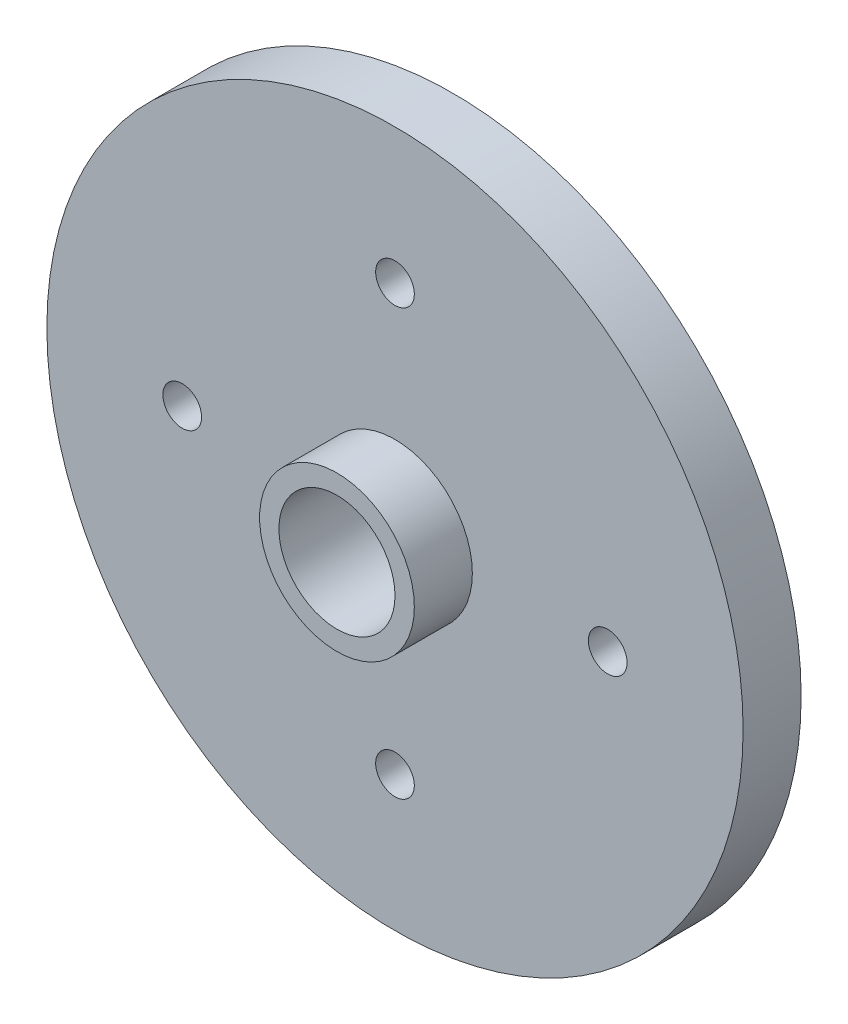
SolidWorks part; units mm, degrees
ref_plane "Front Plane" through (0, 0, 0) normal (0, 0, 1) x (1, 0, 0)
ref_plane "Top Plane" through (0, 0, 0) normal (0, 1, 0) x (1, 0, 0)
ref_plane "Right Plane" through (0, 0, 0) normal (1, 0, 0) x (0, 0, -1)
sketch "Sketch1" plane through (0, 0, 0) normal (0, 0, 1) x (1, 0, 0)
  circle A0 centre (0, 0) radius 18
  circle A1 centre (0, 11) radius 1
  circle A2 centre (11, 0) radius 1
  circle A3 centre (0, -11) radius 1
  circle A4 centre (-11, 0) radius 1
  point P14 (0, 0)
  dimension "D1" = 11
  dimension "D2" = 4
extrude "Boss-Extrude1" add sketch "Sketch1" along normal blind 3
sketch "Sketch2" plane through (0, 0, 3) normal (0, 0, 1) x (1, 0, 0)
  circle A0 centre (0, 0) radius 3
  circle A1 centre (0, 0) radius 4
extrude "Boss-Extrude2" add sketch "Sketch2" along normal blind 3
sketch "Sketch3" plane through (0, 0, 3) normal (0, 0, 1) x (1, 0, 0)
  circle A0 centre (0, 0) radius 3
extrude "Cut-Extrude1" cut sketch "Sketch3" against normal blind 5
